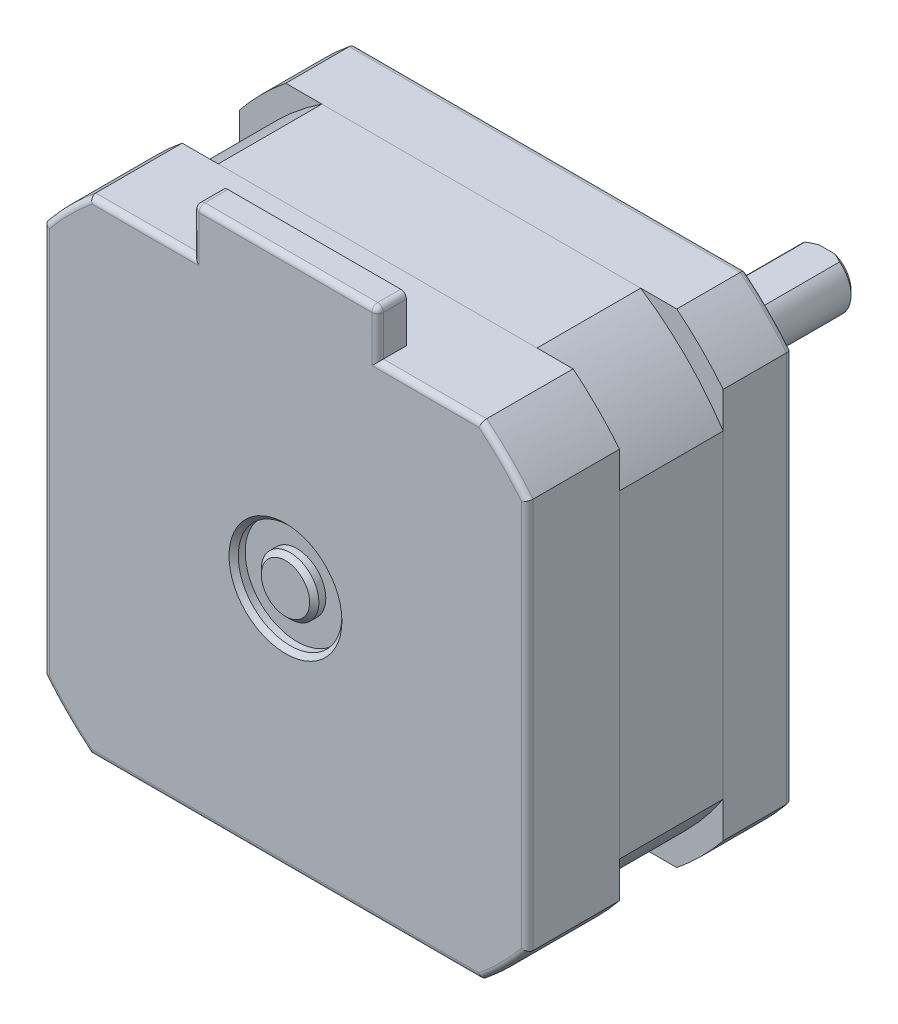
SolidWorks part; units mm, degrees
ref_plane "Plan de face" through (0, 0, 0) normal (0, 0, 1) x (1, 0, 0)
ref_plane "Plan de dessus" through (0, 0, 0) normal (0, 1, 0) x (1, 0, 0)
ref_plane "Plan de droite" through (0, 0, 0) normal (1, 0, 0) x (0, 0, -1)
sketch "Esquisse1" plane through (0, 0, 0) normal (0, 0, 1) x (1, 0, 0)
  line L0 (21, 16.9706) -> (21, -16.9706)
  line L1 (-21, 21) -> (21, 21) construction
  line L2 (-21, 21) -> (-21, -21) construction
  line L3 (-21, -21) -> (21, -21) construction
  line L4 (21, 21) -> (21, -21) construction
  line L5 (-21, 21) -> (21, -21) construction
  line L6 (-21, -21) -> (21, 21) construction
  line L7 (16.9706, -21) -> (-16.9706, -21)
  line L8 (-21, -16.9706) -> (-21, 16.9706)
  line L9 (-16.9706, 21) -> (16.9706, 21)
  arc A0 (-16.9706, 21) -> (-21, 16.9706) centre (0, 0) ccw
  arc A1 (21, 16.9706) -> (16.9706, 21) centre (0, 0) ccw
  arc A2 (-21, -16.9706) -> (-16.9706, -21) centre (0, 0) ccw
  arc A3 (16.9706, -21) -> (21, -16.9706) centre (0, 0) ccw
  point P0 (0, 0)
  dimension "D2" = 54
  dimension "D1" = 42
extrude "Boss.-Extru.1" add sketch "Esquisse1" along normal blind 6
sketch "Esquisse2" plane through (0, 0, 6) normal (0, 0, 1) x (1, 0, 0)
  line L23 (-13.8392, 21) -> (13.8392, 21)
  line L24 (16.9706, 21) -> (-16.9706, 21) construction
  line L25 (21, 13.8392) -> (21, -13.8392)
  line L26 (21, -16.9706) -> (21, 16.9706) construction
  line L27 (13.8392, -21) -> (-13.8392, -21)
  line L28 (-16.9706, -21) -> (16.9706, -21) construction
  line L29 (-21, -13.8392) -> (-21, 13.8392)
  line L30 (-21, 16.9706) -> (-21, -16.9706) construction
  arc A60 (-13.8392, 21) -> (-21, 13.8392) centre (0, 0) ccw
  arc A61 (21, 16.9706) -> (16.9706, 21) centre (0, 0) ccw construction
  arc A62 (21, 13.8392) -> (13.8392, 21) centre (0, 0) ccw
  arc A63 (13.8392, -21) -> (21, -13.8392) centre (0, 0) ccw
  arc A64 (-21, -13.8392) -> (-13.8392, -21) centre (0, 0) ccw
  dimension "D1" = 1.85
extrude "Boss.-Extru.2" add sketch "Esquisse2" along normal blind 9 separate body
sketch "Esquisse3" plane through (0, 0, 15) normal (0, 0, 1) x (1, 0, 0)
  line L0 (-16.9706, -21) -> (16.9706, -21) construction
  line L1 (21, -16.9706) -> (21, 16.9706) construction
  line L2 (16.9706, 21) -> (-16.9706, 21) construction
  line L3 (-21, 16.9706) -> (-21, -16.9706) construction
  line L4 (-16.9706, -21) -> (16.9706, -21)
  line L5 (21, -16.9706) -> (21, 16.9706)
  line L6 (16.9706, 21) -> (-16.9706, 21)
  line L7 (-21, 16.9706) -> (-21, -16.9706)
  arc A0 (-21, -16.9706) -> (-16.9706, -21) centre (0, 0) ccw construction
  arc A1 (16.9706, -21) -> (21, -16.9706) centre (0, 0) ccw construction
  arc A2 (21, 16.9706) -> (16.9706, 21) centre (0, 0) ccw construction
  arc A3 (-16.9706, 21) -> (-21, 16.9706) centre (0, 0) ccw construction
  arc A4 (-21, -16.9706) -> (-16.9706, -21) centre (0, 0) ccw
  arc A5 (16.9706, -21) -> (21, -16.9706) centre (0, 0) ccw
  arc A6 (21, 16.9706) -> (16.9706, 21) centre (0, 0) ccw
  arc A7 (-16.9706, 21) -> (-21, 16.9706) centre (0, 0) ccw
extrude "Boss.-Extru.3" add sketch "Esquisse3" along normal blind 8 separate body
sketch "Esquisse4" plane through (0, 21, 0) normal (0, 1, 0) x (1, 0, 0)
  line L0 (16.9706, -23) -> (-16.9706, -23) construction
  line L1 (8, -23) -> (-8, -23)
  line L2 (8, -23) -> (8, -20.5)
  line L3 (8, -20.5) -> (-8, -20.5)
  line L4 (-8, -23) -> (-8, -20.5)
  line L5 (0, 0) -> (0, -20.5) construction
  dimension "D1" = 2.5
  dimension "D2" = 16
extrude "Boss.-Extru.4" add sketch "Esquisse4" along normal blind 4
sketch "Esquisse5" plane through (0, 0, 0) normal (1, 0, 0) x (0, 0, -1)
  line L0 (0, 0) -> (-78.698, 0) construction
  line L2 (2, 11) -> (0, 11)
  line L3 (2, 11) -> (2, 4.5)
  line L4 (2, 4.5) -> (0, 4.5)
  line L5 (0, 11) -> (0, 4.5)
  line L6 (0, -16.9706) -> (0, 16.9706) construction
  line L7 (24, 0) -> (0, 0)
  line L8 (24, 0) -> (24, 2.5)
  line L9 (24, 2.5) -> (0, 2.5)
  line L10 (0, 0) -> (0, 2.5)
  dimension "D1" = 2
  dimension "D2" = 22
  dimension "D3" = 9
  dimension "D4" = 5
  dimension "D5" = 24
revolve "Révolution1" add sketch "Esquisse5" angle 360 about L0
fillet "Congé1" radius 0.5 14 edges at (-21, 0, 23) (-19.0919, 19.0919, 23) (-12.4853, 21, 23) (-8, 23, 23) (0, 25, 23) (8, 23, 23) (12.4853, 21, 23) (19.0919, 19.0919, 23) (21, 0, 23) (19.0919, -19.0919, 23) (0, -21, 23) (-19.0919, -19.0919, 23) (-8, 25, 21.75) (8, 25, 21.75)
fillet "Congé2" radius 0.5 8 edges at (-19.0919, 19.0919, 0) (-21, 0, 0) (-19.0919, -19.0919, 0) (0, -21, 0) (19.0919, -19.0919, 0) (21, 0, 0) (0, 21, 0) (19.0919, 19.0919, 0)
chamfer "Chanfrein1" distance 0.4 angle 45 1 edges at (-2.5, 0, -24)
chamfer "Chanfrein2" distance 0.4 angle 45 1 edges at (-4.5, 0, -2)
sketch "Esquisse6" plane through (0, 0, 0) normal (1, 0, 0) x (0, 0, -1)
  line L0 (0, -2.5) -> (23.6, -2.5) construction
  line L1 (24, 2.5) -> (9, 2.5)
  line L2 (24, 2.5) -> (24, 2)
  line L3 (24, 2) -> (9, 2)
  line L4 (9, 2.5) -> (9, 2)
  line L5 (24, -2.1) -> (24, 2.1) construction
  line L6 (23.6, 2.5) -> (0, 2.5) construction
  dimension "D1" = 4.5
  dimension "D2" = 15
extrude "Enlèv. mat.-Extru.1" cut sketch "Esquisse6" against normal through all both and the other way through all
sketch "Esquisse7" plane through (0, 0, 23) normal (0, 0, 1) x (1, 0, 0)
  circle A0 centre (0, 0) radius 2.5
  circle A1 centre (0, 0) radius 4.5
  dimension "D1" = 5
  dimension "D2" = 9
extrude "Enlèv. mat.-Extru.2" cut sketch "Esquisse7" against normal blind 1
chamfer "Chanfrein3" distance 0.4 angle 45 2 edges at (4.5, 0, 23) (2.5, 0, 23)
hole_wizard "Trou taraudé M31" positions "Esquisse8" profile "Esquisse9" tap size "M3" standard "ISO"
sketch "Esquisse8" plane through (0, 0, 0) normal (0, 0, -1) x (-1, 0, 0)
  line L0 (-15.5, 15.5) -> (15.5, 15.5) construction
  line L1 (15.5, 15.5) -> (15.5, -15.5) construction
  line L2 (15.5, -15.5) -> (-15.5, -15.5) construction
  line L3 (-15.5, -15.5) -> (-15.5, 15.5) construction
  circle A0 centre (0, 0) radius 21.9203 construction
  point P5 (-15.5, 15.5)
  point P6 (15.5, 15.5)
  point P7 (15.5, -15.5)
  point P8 (-15.5, -15.5)
  dimension "D1" = 31
sketch "Esquisse9" plane through (15.5, -15.5, 0) normal (1, 0, 0) x (0, 1, 0)
  line L0 (0, 0) -> (0, 5.7511)
  line L1 (0, 5.7511) -> (1.25, 5)
  line L2 (1.25, 5) -> (1.25, 0)
  line L5 (1.25, 0) -> (0, 0)
  line L10 (0, 5.7511) -> (-1.25, 5) construction
  line L11 (0, -6.35) -> (0, 107.95) construction
  dimension "Diamètre du trou pour taraudage" = 2.5
  dimension "Profondeur du trou pour taraudage" = 5
  dimension "Angle de pointe" = 118
cosmetic thread "Filetage de perçage1" parameters "D1"=5, "D2"=3
cosmetic thread "Filetage de perçage2" parameters "D1"=5, "D2"=3
cosmetic thread "Filetage de perçage3" parameters "D1"=5, "D2"=3
cosmetic thread "Filetage de perçage4" parameters "D1"=5, "D2"=3
